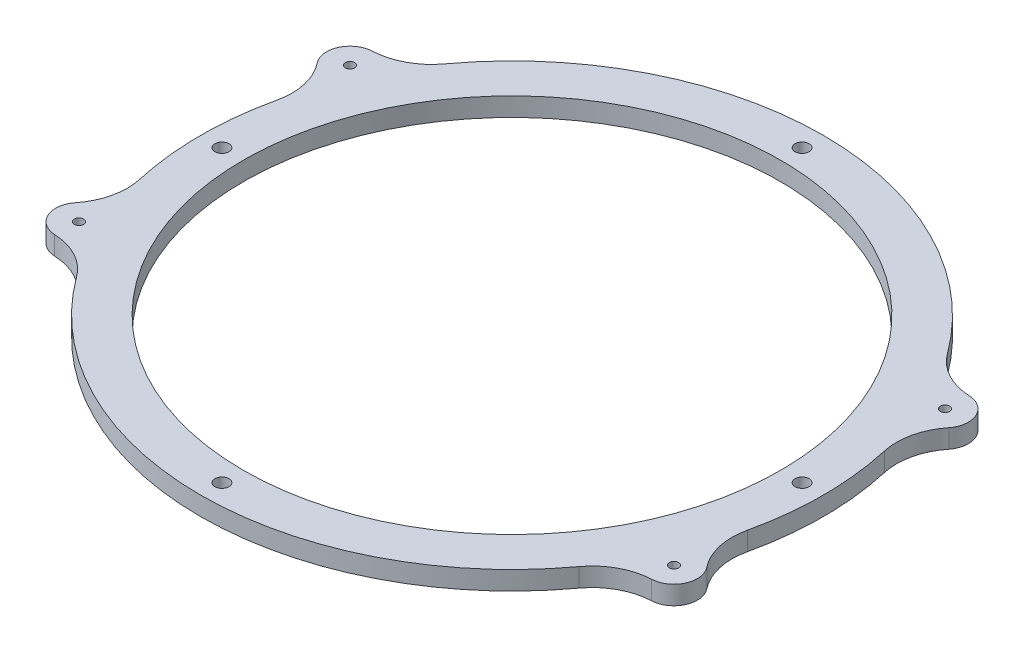
SolidWorks part; units mm, degrees
ref_plane "Front Plane" through (0, 0, 0) normal (0, 0, 1) x (1, 0, 0)
ref_plane "Top Plane" through (0, 0, 0) normal (0, 1, 0) x (1, 0, 0)
ref_plane "Right Plane" through (0, 0, 0) normal (1, 0, 0) x (0, 0, -1)
sketch "Sketch1" plane through (0, 0, 0) normal (0, 1, 0) x (1, 0, 0)
  line L0 (75.9934, 65) -> (110, 65)
  line L1 (-110, 65) -> (-75.9934, 65)
  line L2 (-110, 65) -> (-110, -65)
  line L3 (-110, -65) -> (-75.9934, -65)
  line L4 (110, 65) -> (110, -65)
  line L5 (-110, 65) -> (110, -65) construction
  line L6 (-110, -65) -> (110, 65) construction
  line L7 (75.9934, -65) -> (110, -65)
  circle A0 centre (0, 0) radius 86.25
  arc A3 (-75.9934, -65) -> (75.9934, -65) centre (0, 0) ccw
  arc A4 (75.9934, 65) -> (-75.9934, 65) centre (0, 0) ccw
  point P0 (0, 0)
  dimension "D3" = 172.5
  dimension "D5" = 200
  dimension "D1" = 220
  dimension "D2" = 130
extrude "Boss-Extrude1" add sketch "Sketch1" along normal blind 6
sketch "Sketch2" plane through (0, 0, 0) normal (0, 1, 0) x (1, 0, 0)
  line L0 (0, -3.3) -> (0, 3.3) construction
  line L1 (-3.3, 0) -> (3.3, 0) construction
  circle A0 centre (-95.5, 43.5) radius 1.5
  circle A1 centre (95.5, 43.5) radius 1.5
  circle A2 centre (95.5, -43.5) radius 1.5
  circle A3 centre (-95.5, -43.5) radius 1.5
  dimension "D1" = 3
  dimension "D2" = 95.5
  dimension "D3" = 43.5
extrude "Cut-Extrude1" cut sketch "Sketch2" along normal blind 6
sketch "Sketch3" plane through (0, 0, 0) normal (0, 1, 0) x (1, 0, 0)
  circle A1 centre (0, 93.125) radius 2.25
  circle A2 centre (93.125, 0) radius 2.25
  circle A3 centre (0, -93.125) radius 2.25
  circle A4 centre (-93.125, 0) radius 2.25
  point P13 (0, 0)
  dimension "D1" = 4.5
  dimension "D2" = 93.125
  dimension "D3" = 4
extrude "Cut-Extrude2" cut sketch "Sketch3" along normal blind 6
sketch "Sketch4" plane through (0, 0, 0) normal (0, 1, 0) x (1, 0, 0)
  line L1 (0, -3.3) -> (0, 3.3) construction
  line L6 (98.6089, -36.6747) -> (93.8566, -34.51)
  line L11 (-95.5, 43.5) -> (0, 0) construction
  line L12 (-98.6089, 36.6747) -> (-93.8566, 34.51)
  line L13 (-92.3911, 50.3253) -> (-87.6388, 48.1606)
  line L14 (92.3911, -50.3253) -> (87.6388, -48.1606)
  line L15 (75.9934, -65) -> (110, -65)
  line L16 (-75.9934, 65) -> (-110, 65)
  line L17 (-110, 65) -> (-110, -65)
  line L18 (110, 65) -> (110, -65)
  line L20 (-3.3, 0) -> (3.3, 0) construction
  line L21 (-75.9934, -65) -> (-110, -65)
  line L22 (-92.3911, -50.3253) -> (-87.6388, -48.1606)
  line L23 (-98.6089, -36.6747) -> (-93.8566, -34.51)
  line L24 (75.9934, 65) -> (110, 65)
  line L25 (92.3911, 50.3253) -> (87.6388, 48.1606)
  line L26 (98.6089, 36.6747) -> (93.8566, 34.51)
  arc A0 (75.9934, -65) -> (87.6388, -48.1606) centre (0, 0) ccw
  arc A1 (-75.9934, 65) -> (-87.6388, 48.1606) centre (0, 0) ccw
  arc A2 (-92.3911, 50.3253) -> (-98.6089, 36.6747) centre (-95.5, 43.5) ccw
  arc A3 (-93.8566, 34.51) -> (-93.8566, -34.51) centre (0, 0) ccw
  arc A4 (-92.3911, -50.3253) -> (-98.6089, -36.6747) centre (-95.5, -43.5) cw
  arc A5 (-75.9934, -65) -> (-87.6388, -48.1606) centre (0, 0) cw
  arc A6 (92.3911, -50.3253) -> (98.6089, -36.6747) centre (95.5, -43.5) ccw
  arc A7 (93.8566, 34.51) -> (93.8566, -34.51) centre (0, 0) cw
  arc A8 (92.3911, 50.3253) -> (98.6089, 36.6747) centre (95.5, 43.5) cw
  arc A9 (75.9934, 65) -> (87.6388, 48.1606) centre (0, 0) cw
  point P20 (0, 0)
  dimension "D1" = 100
  dimension "D2" = 7.5
  dimension "D3" = 7.5
extrude "Cut-Extrude3" cut sketch "Sketch4" along normal blind 6
fillet "Fillet1" radius 20 8 edges at (87.6388, 3, -48.1606) (93.8566, 3, -34.51) (93.8566, 3, 34.51) (87.6388, 3, 48.1606) (-87.6388, 3, 48.1606) (-93.8566, 3, 34.51) (-93.8566, 3, -34.51) (-87.6388, 3, -48.1606)
